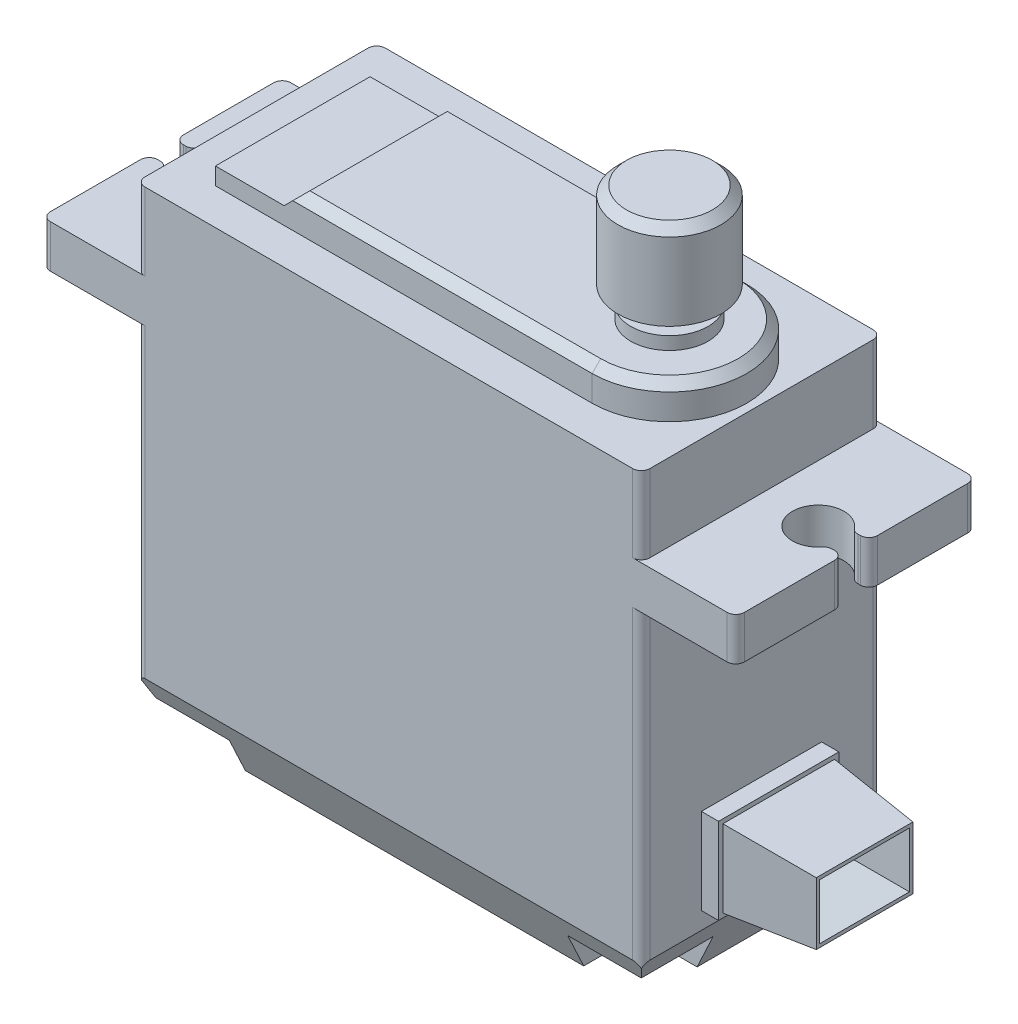
SolidWorks part; units mm, degrees
material "PE High Density"
ref_plane "Alzado" through (0, 0, 0) normal (0, 0, 1) x (1, 0, 0)
ref_plane "Planta" through (0, 0, 0) normal (0, 1, 0) x (1, 0, 0)
ref_plane "Vista lateral" through (0, 0, 0) normal (1, 0, 0) x (0, 0, -1)
sketch "Croquis1" plane through (0, 0, 0) normal (0, 0, 1) x (1, 0, 0)
  line L1 (-14.7, -14) -> (14.7, -14)
  line L2 (-14.7, -14) -> (-14.7, 14)
  line L3 (-14.7, 14) -> (14.7, 14)
  line L4 (14.7, -14) -> (14.7, 14)
  line L5 (-14.7, -14) -> (14.7, 14) construction
  line L6 (-14.7, 14) -> (14.7, -14) construction
  point P0 (0, 0)
  dimension "D1" = 29.4
  dimension "D2" = 28
extrude "Saliente-Extruir1" add sketch "Croquis1" along normal mid plane 14
ref_plane "Plano1" through (0, 0, 9.25) normal (0, 0, 1) x (1, 0, 0)
sketch "Croquis2" plane through (0, 0, 7) normal (0, 0, 1) x (1, 0, 0)
  line L0 (14.7, 14) -> (-14.7, 14) construction
  line L1 (-14.7, 9.5) -> (-20.2, 9.5)
  line L2 (-14.7, 9.5) -> (-14.7, 7)
  line L3 (-14.7, 7) -> (-20.2, 7)
  line L4 (-20.2, 9.5) -> (-20.2, 7)
  line L5 (-14.7, -14) -> (14.7, -14) construction
  line L6 (0, 14) -> (0, -14) construction
  line L7 (14.7, 14) -> (-14.7, 14) construction
  line L8 (14.7, 9.5) -> (14.7, 7)
  line L9 (14.7, 7) -> (20.2, 7)
  line L10 (20.2, 9.5) -> (20.2, 7)
  line L11 (14.7, 9.5) -> (20.2, 9.5)
  line L12 (-14.7, 14) -> (-14.7, -14) construction
  dimension "D1" = 2.5
  dimension "D2" = 5.5
  dimension "D3" = 4.5
extrude "Saliente-Extruir2" add sketch "Croquis2" against normal up to surface (14 mm away) up to face at (0, 0, -7)
sketch "Croquis4" plane through (0, 9.5, 0) normal (0, 1, 0) x (1, 0, 0)
  line L0 (-20.2, 0.75) -> (-19.299, 0.75)
  line L1 (0, 0) -> (0, 7) construction
  line L2 (-18, -10) -> (-18, 0) construction
  line L3 (-18, 0) -> (18, 0) construction
  line L4 (14.7, 7) -> (-14.7, 7) construction
  line L5 (20.2, 0) -> (18, 0) construction
  line L6 (20.2, -0.75) -> (20.2, 0.75)
  line L7 (-20.2, 7) -> (-20.2, -7) construction
  line L8 (-20.2, -0.75) -> (-19.299, -0.75)
  line L9 (20.2, -0.75) -> (19.299, -0.75)
  line L11 (20.2, 0.75) -> (19.299, 0.75)
  line L21 (-20.2, -0.75) -> (-20.2, 0.75)
  line L22 (-20.2, 0) -> (-18, 0) construction
  arc A0 (19.299, -0.75) -> (19.299, 0.75) centre (18, 0) cw
  arc A3 (-19.299, -0.75) -> (-19.299, 0.75) centre (-18, 0) ccw
  point P0 (0, 0)
  dimension "D3" = 3
  dimension "D1" = 36
  dimension "D2" = 1.5
extrude "Cortar-Extruir1" cut sketch "Croquis4" against normal up to vertex (2.5 mm away)
chamfer "Chaflán1" distance 1.5 angle 65 4 edges at (0, -14, -7) (0, -14, 7) (-14.7, -14, 0) (14.7, -14, 0)
sketch "Croquis5" plane through (0, -14, 0) normal (0, -1, 0) x (1, 0, 0)
  line L0 (-11.85, 0) -> (11.85, 0) construction
  line L1 (-11.85, -4.25) -> (11.85, -4.25) construction
  line L2 (-11.85, -4.25) -> (-11.85, 4.25) construction
  line L3 (-11.85, 4.25) -> (11.85, 4.25) construction
  line L4 (11.85, -4.25) -> (11.85, 4.25) construction
  line L5 (-11.85, -4.25) -> (11.85, 4.25) construction
  line L6 (-11.85, 4.25) -> (11.85, -4.25) construction
  line L7 (0, 4.25) -> (0, -4.25) construction
  line L8 (-14.7, 2.25) -> (-11.85, 2.25)
  line L9 (-13.2, 5.5) -> (-13.2, -5.5) construction
  line L10 (-9.85, 4.25) -> (-9.85, 7)
  line L11 (13.2, 5.5) -> (-13.2, 5.5) construction
  line L12 (-14.7, 7) -> (14.7, 7) construction
  line L13 (-14.7, -7) -> (-14.7, 7) construction
  line L14 (-9.85, 7) -> (-14.7, 7)
  line L15 (-14.7, 7) -> (-14.7, 2.25)
  line L16 (-14.7, -7) -> (-14.7, -2.25)
  line L17 (-9.85, -7) -> (-14.7, -7)
  line L18 (-9.85, -4.25) -> (-9.85, -7)
  line L19 (-14.7, -2.25) -> (-11.85, -2.25)
  line L20 (14.7, -2.25) -> (11.85, -2.25)
  line L21 (9.85, -4.25) -> (9.85, -7)
  line L22 (9.85, -7) -> (14.7, -7)
  line L23 (14.7, -7) -> (14.7, -2.25)
  line L24 (14.7, 7) -> (14.7, 2.25)
  line L25 (9.85, 7) -> (14.7, 7)
  line L26 (9.85, 4.25) -> (9.85, 7)
  line L27 (14.7, 2.25) -> (11.85, 2.25)
  arc A0 (-11.85, 2.25) -> (-9.85, 4.25) centre (-11.85, 4.25) ccw
  arc A1 (-11.85, -2.25) -> (-9.85, -4.25) centre (-11.85, -4.25) cw
  arc A2 (11.85, -2.25) -> (9.85, -4.25) centre (11.85, -4.25) ccw
  arc A3 (11.85, 2.25) -> (9.85, 4.25) centre (11.85, 4.25) cw
  point P0 (0, 0)
  dimension "D3" = 2
  dimension "D1" = 1.35
  dimension "D2" = 1.25
extrude "Cortar-Extruir2" cut sketch "Croquis5" against normal blind 2
sketch "Croquis6" plane through (0, 14, 0) normal (0, 1, 0) x (1, 0, 0)
  line L1 (14.7, 7) -> (-14.7, 7) construction
  line L2 (-14.7, -7) -> (-14.7, 7) construction
  line L3 (14.7, -7) -> (-14.7, -7) construction
  line L4 (14.7, -7) -> (14.7, 7) construction
  line L5 (14.7, 7) -> (-14.7, 7) construction
  line L6 (-14.7, -7) -> (-14.7, 7) construction
  line L7 (14.7, -7) -> (-14.7, -7) construction
  line L8 (14.7, -7) -> (14.7, 7) construction
  line L9 (9.73, 4.11) -> (-12.2, 4.11)
  line L10 (-12.2, -4.89) -> (-12.2, 4.11)
  line L11 (9.73, -4.89) -> (-12.2, -4.89)
  arc A0 (9.73, -4.89) -> (9.73, 4.11) centre (9.73, -0.39) ccw
  dimension "D2" = 4.97
  dimension "D1" = 6.61
  dimension "D3" = 2.5
  dimension "D4" = 4.22
extrude "Saliente-Extruir4" add sketch "Croquis6" along normal blind 2
sketch "Croquis9" plane through (0, 0, 4.89) normal (0, 0, 1) x (1, 0, 0)
  line L0 (-12.2, 16) -> (-12.2, 15)
  line L2 (-12.2, 15) -> (-8.2, 15)
  line L3 (-8.2, 15) -> (-7.2, 16)
  line L5 (-7.2, 16) -> (-12.2, 16)
  line L7 (-12.2, 16) -> (-12.2, 14) construction
  line L8 (-12.2, 16) -> (9.73, 16) construction
  dimension "D1" = 5
  dimension "D2" = 45
extrude "Cortar-Extruir3" cut sketch "Croquis9" against normal up to vertex
sketch "Croquis10" plane through (0, 16, 0) normal (0, 1, 0) x (1, 0, 0)
  arc A0 (9.73, -4.89) -> (9.73, 4.11) centre (9.73, -0.39) ccw construction
  circle A1 centre (9.73, -0.39) radius 2.25
  arc A2 (9.73, -4.89) -> (9.73, 4.11) centre (9.73, -0.39) ccw construction
  dimension "D1" = 2.25
extrude "Saliente-Extruir5" add sketch "Croquis10" along normal blind 0.75
sketch "Croquis11" plane through (0, 16.75, 0) normal (0, 1, 0) x (1, 0, 0)
  circle A0 centre (9.73, -0.39) radius 0.75
  circle A1 centre (9.73, -0.39) radius 2.25
  circle A2 centre (9.73, -0.39) radius 2.25 construction
  dimension "D1" = 0
  dimension "D2" = 1.5
extrude "Saliente-Extruir6" add sketch "Croquis11" along normal blind 1
sketch "Croquis12" plane through (0, 17.75, 0) normal (0, 1, 0) x (1, 0, 0)
  circle A0 centre (9.73, -0.39) radius 3
  circle A1 centre (9.73, -0.39) radius 0.75 construction
  dimension "D1" = 6
extrude "Saliente-Extruir7" add sketch "Croquis12" along normal blind 5
sketch "Croquis14" plane through (14.7, 0, 0) normal (1, 0, 0) x (0, 0, -1)
  line L0 (0, 0) -> (0, -7.2832) construction
  line L1 (-3.5, -9.7832) -> (3.5, -9.7832)
  line L2 (-3.5, -9.7832) -> (-3.5, -4.7832)
  line L3 (-3.5, -4.7832) -> (3.5, -4.7832)
  line L4 (3.5, -9.7832) -> (3.5, -4.7832)
  line L5 (-3.5, -9.7832) -> (3.5, -4.7832) construction
  line L6 (-3.5, -4.7832) -> (3.5, -9.7832) construction
  line L7 (-7, -10.7832) -> (7, -10.7832) construction
  point P0 (0, -7.2832)
  dimension "D1" = 7
  dimension "D2" = 5
  dimension "D3" = 3.5
extrude "Saliente-Extruir8" add sketch "Croquis14" along normal blind 1
sketch "Croquis15" plane through (15.7, 0, 0) normal (1, 0, 0) x (0, 0, -1)
  line L0 (3.25, -5.0332) -> (-3.25, -5.0332)
  line L1 (-3.25, -5.0332) -> (-3.25, -9.5332)
  line L2 (-3.25, -9.5332) -> (3.25, -9.5332)
  line L3 (3.25, -9.5332) -> (3.25, -5.0332)
  line L4 (3.5, -9.7832) -> (3.5, -4.7832)
  line L5 (3.5, -4.7832) -> (-3.5, -4.7832)
  line L6 (-3.5, -4.7832) -> (-3.5, -9.7832)
  line L7 (-3.5, -9.7832) -> (3.5, -9.7832)
  line L8 (3.5, -9.7832) -> (3.5, -4.7832) construction
  line L9 (3.5, -4.7832) -> (-3.5, -4.7832) construction
  line L10 (-3.5, -4.7832) -> (-3.5, -9.7832) construction
  line L11 (-3.5, -9.7832) -> (3.5, -9.7832) construction
  dimension "D1" = 0
  dimension "D2" = 0.25
extrude "Saliente-Extruir9" add sketch "Croquis15" along normal blind 5 draft 5 separate body
shell "Vaciado2" thickness 0.2
chamfer "Chaflán2" distance 0.5 angle 45 1 edges at (9.73, 22.75, 3.39)
fillet "Fillet1" radius 0.5 20 edges at (20.2, 8.25, -7) (19.299, 8.25, 0.75) (19.299, 8.25, -0.75) (20.2, 8.25, -0.75) (20.2, 8.25, 0.75) (20.2, 8.25, 7) (-19.299, 8.25, -0.75) (-20.2, 8.25, 7) (-19.299, 8.25, 0.75) (-20.2, 8.25, 0.75) (-20.2, 8.25, -0.75) (-20.2, 8.25, -7)
